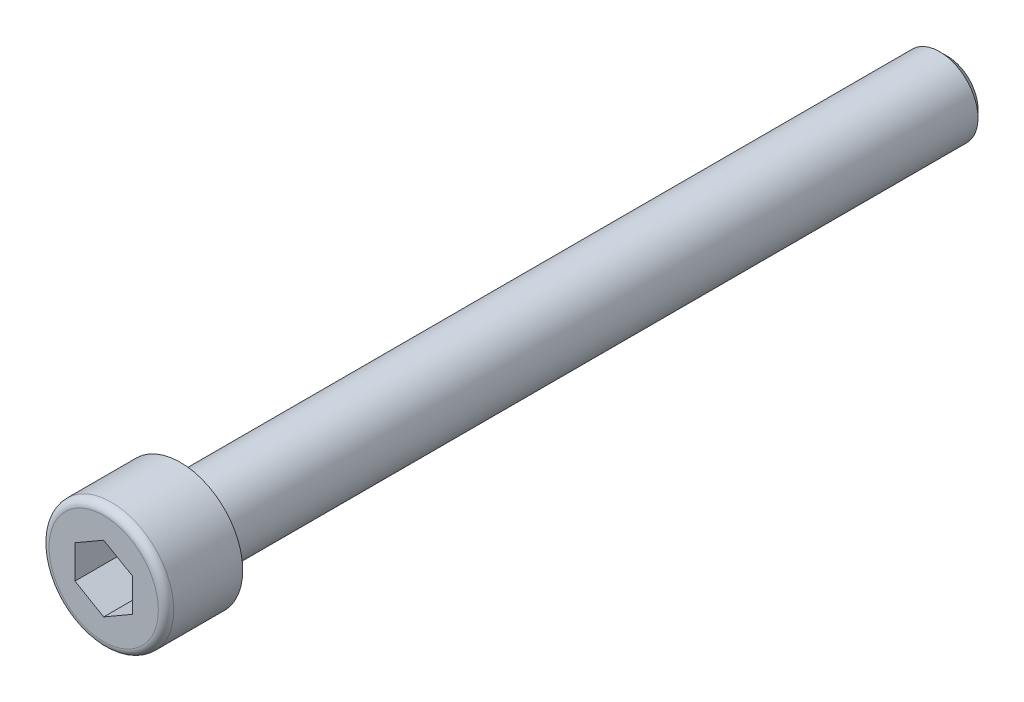
SolidWorks part; units mm, degrees
ref_plane "Přední" through (0, 0, 0) normal (0, 0, 1) x (1, 0, 0)
ref_plane "Horní" through (0, 0, 0) normal (0, 1, 0) x (1, 0, 0)
ref_plane "Pravá" through (0, 0, 0) normal (1, 0, 0) x (0, 0, -1)
sketch "Skica1" plane through (0, 0, 0) normal (0, 1, 0) x (1, 0, 0)
  line L0 (0, 80) -> (0, -8)
  line L1 (0, -8) -> (5.7, -8)
  line L2 (6.5, -7.2) -> (6.5, 0)
  line L3 (6.5, 0) -> (4, 0)
  line L4 (4, 0) -> (4, 79.2)
  line L5 (3.2, 80) -> (0, 80)
  line L6 (4, 79.2) -> (3.2, 80)
  line L8 (0, 20.5555) -> (0, 32.1314) construction
  arc A0 (5.7, -8) -> (6.5, -7.2) centre (5.7, -7.2) ccw
  arc A1 (3.2, 80) -> (4, 79.2) centre (3.2, 79.2) cw construction
  dimension "D5" = 0.8
  dimension "D6" = 0.8
  dimension "D1" = 8
  dimension "D2" = 80
  dimension "D3" = 8
  dimension "D4" = 13
revolve "Základ-Rotační" add sketch "Skica1" angle 360 about L8
cosmetic thread "Kosmetický závit1" parameters "D1"=28, "D2"=6.6
sketch "Skica2" plane through (0, 0, 8) normal (0, 0, 1) x (1, 0, 0)
  line L1 (3, -1.7321) -> (3, 1.7321)
  line L2 (3, 1.7321) -> (0, 3.4641)
  line L3 (0, 3.4641) -> (-3, 1.7321)
  line L4 (-3, 1.7321) -> (-3, -1.7321)
  line L5 (-3, -1.7321) -> (0, -3.4641)
  line L6 (0, -3.4641) -> (3, -1.7321)
  circle A0 centre (0, 0) radius 3 construction
  dimension "D1" = 6
extrude "Odebrání-Protažení1" cut sketch "Skica2" against normal blind 6
